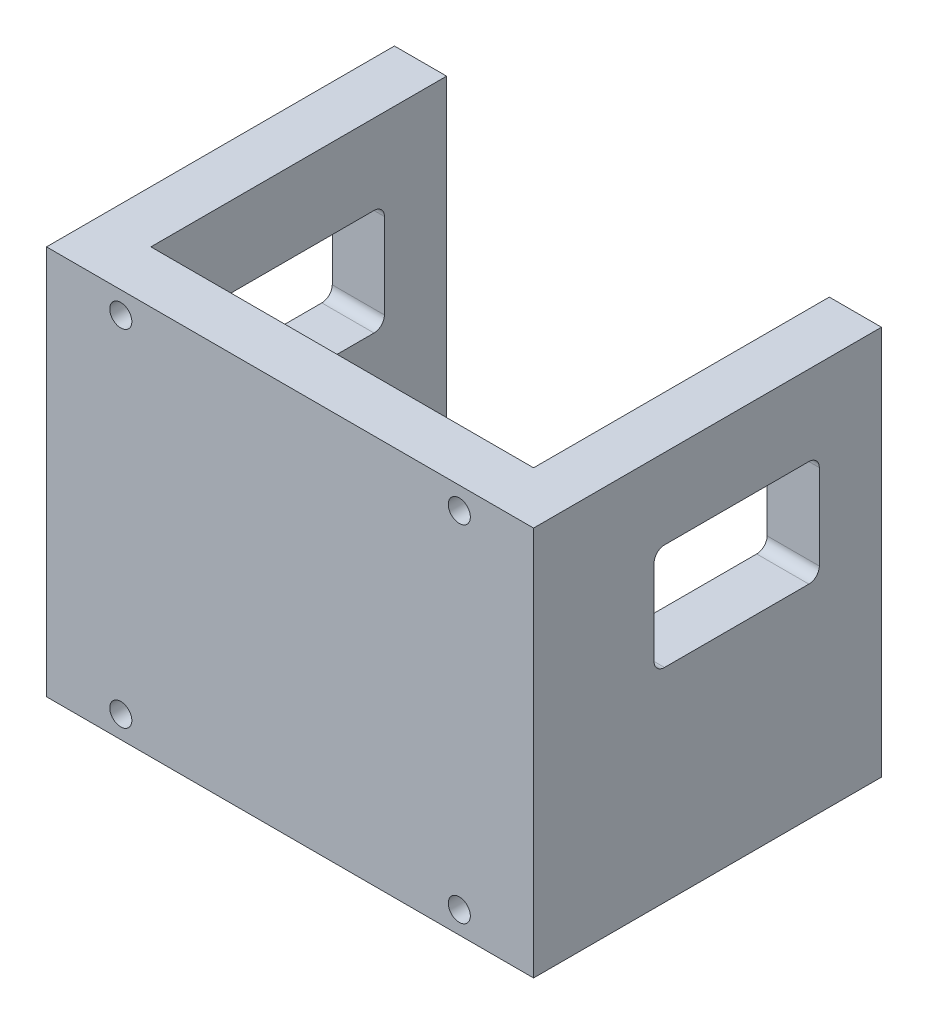
SolidWorks part; units mm, degrees
ref_plane "Plan de face" through (0, 0, 0) normal (0, 0, 1) x (1, 0, 0)
ref_plane "Plan de dessus" through (0, 0, 0) normal (0, 1, 0) x (1, 0, 0)
ref_plane "Plan de droite" through (0, 0, 0) normal (1, 0, 0) x (0, 0, -1)
sketch "Esquisse1" plane through (0, 0, 0) normal (0, 0, 1) x (1, 0, 0)
  line L0 (-109.5296, 4.4139) -> (30.4704, 4.4139)
  line L1 (-109.5296, 4.4139) -> (-109.5296, -107.5861)
  line L2 (-109.5296, -107.5861) -> (30.4704, -107.5861)
  line L3 (30.4704, -107.5861) -> (30.4704, 4.4139)
  dimension "D1" = 140
  dimension "D2" = 112
extrude "Boss.-Extru.1" add sketch "Esquisse1" along normal blind 100
sketch "Esquisse2" plane through (0, 4.4139, 0) normal (0, 1, 0) x (1, 0, 0)
  line L0 (30.4704, 0) -> (-109.5296, 0) construction
  line L1 (-94.5296, 0) -> (15.4704, 0)
  line L2 (-94.5296, 0) -> (-94.5296, -85)
  line L3 (-94.5296, -85) -> (15.4704, -85)
  line L4 (15.4704, 0) -> (15.4704, -85)
  line L5 (-109.5296, -100) -> (-109.5296, 0) construction
  line L6 (30.4704, -100) -> (-109.5296, -100) construction
  line L7 (30.4704, -100) -> (30.4704, 0) construction
  dimension "D1" = 15
  dimension "D2" = 15
  dimension "D3" = 15
extrude "Enlèv. mat.-Extru.1" cut sketch "Esquisse2" against normal through all contours L3 L4 L1 L2
sketch "Esquisse3" plane through (-109.5296, 0, 0) normal (-1, 0, 0) x (0, 0, 1)
  line L0 (58.0675, -19.0982) -> (25.1675, -19.0982) construction
  line L1 (17.8675, -49.0982) -> (65.3675, -49.0982)
  line L2 (17.8675, -49.0982) -> (17.8675, -18.5982)
  line L3 (17.8675, -18.5982) -> (65.3675, -18.5982)
  line L4 (65.3675, -49.0982) -> (65.3675, -18.5982)
  line L5 (64.8675, -40.7982) -> (64.8675, -25.8982) construction
  line L6 (25.1675, -47.5982) -> (58.0675, -47.5982) construction
  line L7 (18.3675, -29.3282) -> (18.3675, -37.3682) construction
  dimension "D1" = 0.5
  dimension "D2" = 0.5
  dimension "D3" = 1.5
  dimension "D4" = 0.5
extrude "Enlèv. mat.-Extru.2" cut sketch "Esquisse3" against normal through all
sketch "Esquisse4" plane through (0, 0, 85) normal (0, 0, -1) x (-1, 0, 0)
  line L0 (-15.4704, -107.5861) -> (-15.4704, 4.4139) construction
  line L1 (94.5296, 4.4139) -> (-15.4704, 4.4139) construction
  circle A0 centre (-9.1204, -1.9361) radius 3.175
  dimension "D1" = 6.35
  dimension "D2" = 6.35
  dimension "D3" = 6.35
extrude "Enlèv. mat.-Extru.3" cut sketch "Esquisse4" against normal through all
sketch "Esquisse6" plane through (0, 0, 85) normal (0, 0, -1) x (-1, 0, 0)
  line L0 (39.5296, 19.4457) -> (39.5296, -119.95) construction
  line L1 (-15.4704, -107.5861) -> (-15.4704, 4.4139) construction
  line L2 (-51.5517, -51.5861) -> (125.9992, -51.5861) construction
  line L4 (94.5296, 4.4139) -> (-15.4704, 4.4139) construction
  dimension "D1" = 55
  dimension "D2" = 56
ref_plane "Plan1" through (-39.5296, 0, 0) normal (1, 0, 0) x (0, -1, 0)
mirror "Symétrie1" about plane through (-39.5296, 0, 0) normal (1, 0, 0) of "Enlèv. mat.-Extru.3"
ref_plane "Plan2" through (0, -51.5861, 0) normal (0, -1, 0) x (-1, 0, 0)
mirror "Symétrie2" about plane through (0, -51.5861, 0) normal (0, -1, 0) of "Symétrie1", "Enlèv. mat.-Extru.3"
fillet "Congé1" radius 3 8 edges at (-102.0296, -18.5982, 65.3675) (-102.0296, -18.5982, 17.8675) (-102.0296, -49.0982, 17.8675) (-102.0296, -49.0982, 65.3675) (22.9704, -49.0982, 65.3675) (22.9704, -18.5982, 65.3675) (22.9704, -49.0982, 17.8675) (22.9704, -18.5982, 17.8675)
equation "\"3mmmm\"=5"
